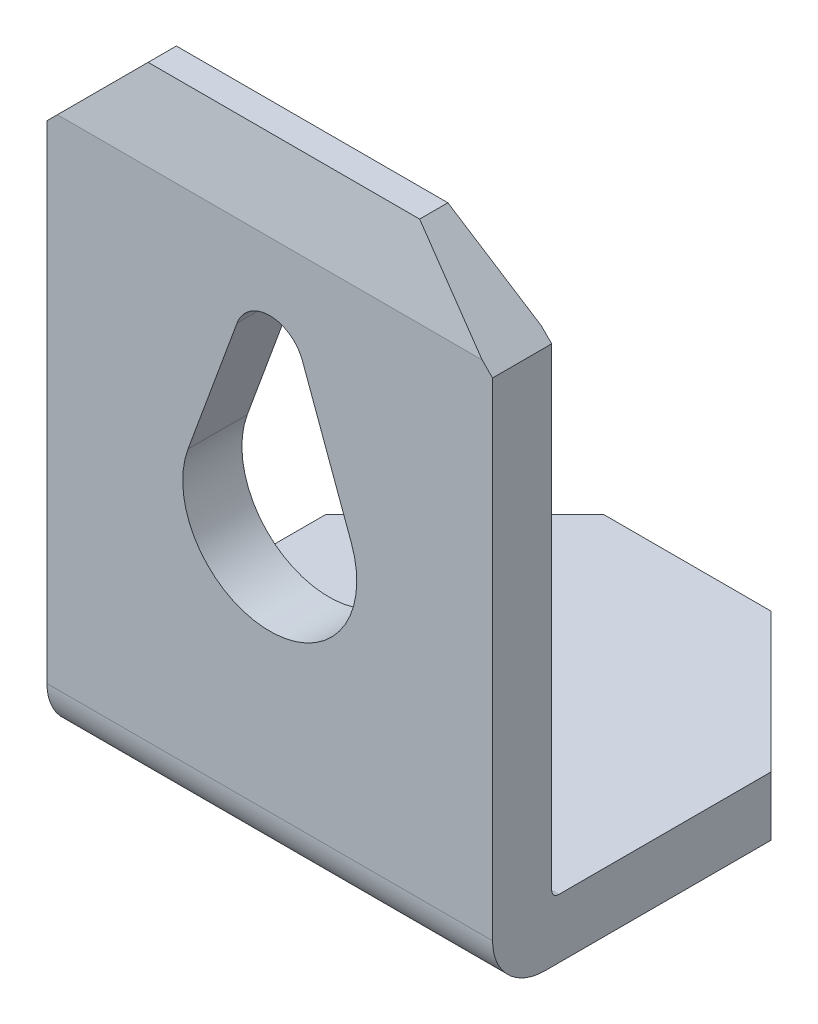
SolidWorks part; units mm, degrees
ref_plane "Front Plane" through (0, 0, 0) normal (0, 0, 1) x (1, 0, 0)
ref_plane "Top Plane" through (0, 0, 0) normal (0, 1, 0) x (1, 0, 0)
ref_plane "Right Plane" through (0, 0, 0) normal (1, 0, 0) x (0, 0, -1)
sketch "Sketch1" plane through (0, 0, 0) normal (1, 0, 0) x (0, 0, -1)
  line L0 (0, 0.1) -> (0, 7.05)
  line L1 (0, 7.05) -> (-0.2414, 8.15)
  line L2 (-0.2414, 8.15) -> (-0.6471, 8.15)
  line L3 (-0.6471, 8.15) -> (-0.85, 7.05)
  line L4 (-0.85, 7.05) -> (-0.85, -0.1)
  line L5 (-0.1, -0.85) -> (5.15, -0.85)
  line L6 (5.15, -0.85) -> (5.15, 0)
  line L7 (5.15, 0) -> (0.1, 0)
  arc A0 (-0.85, -0.1) -> (-0.1, -0.85) centre (-0.1, -0.1) ccw
  arc A1 (0, 0.1) -> (0.1, 0) centre (0.1, 0.1) ccw
  point P3 (5.15, -0.425)
  point P14 (0, 0)
  dimension "D6" = 0.75
  dimension "D7" = 0.1
  dimension "D1" = 9
  dimension "D2" = 0.85
  dimension "D3" = 1.1
  dimension "D5" = 0.85
  dimension "D4" = 6
  dimension "D8" = 0.2414
  dimension "D9" = 0.6471
extrude "Boss-Extrude1" add sketch "Sketch1" along normal blind 6.4
chamfer "Chamfer3" distance 2 angle 45 2 edges at (6.4, -0.425, -5.15) (0, -0.425, -5.15)
sketch "Sketch4" plane through (0, 0, 0.85) normal (0, 0, 1) x (1, 0, 0)
  line L0 (0, 6.9) -> (1.25, 8.15)
  line L1 (0, 7.05) -> (0, -0.1) construction
  line L2 (6.4, 8.15) -> (0, 8.15) construction
  line L4 (5.15, 8.15) -> (6.4, 6.9)
  line L5 (6.4, 7.05) -> (6.4, -0.1) construction
  line L6 (0, 6.9) -> (0, 8.15)
  line L7 (0, 8.15) -> (1.25, 8.15)
  line L8 (5.15, 8.15) -> (6.4, 8.15)
  line L9 (6.4, 8.15) -> (6.4, 6.9)
  dimension "D1" = 1.25
  dimension "D2" = 1.25
  dimension "D3" = 1.25
extrude "Cut-Extrude1" cut sketch "Sketch4" against normal up to surface (0.85 mm away) up to face at (3.2, 3.575, 0)
sketch "Sketch5" plane through (0, 0, 0.85) normal (0, 0, 1) x (1, 0, 0)
  line L0 (5.15, 8.15) -> (1.25, 8.15) construction
  line L1 (2.7306, 5.7488) -> (2.0266, 3.8307)
  line L2 (3.6696, 5.7481) -> (4.3734, 3.8307)
  line L3 (0, 6.9) -> (0, -0.1) construction
  arc A0 (2.0266, 3.8307) -> (4.3734, 3.8307) centre (3.2, 3.4) ccw
  arc A1 (3.6696, 5.7481) -> (2.7306, 5.7488) centre (3.2, 5.5765) ccw
  dimension "D1" = 2.5
  dimension "D3" = 1
  dimension "D2" = 4.75
  dimension "D4" = 2.1765
  dimension "D5" = 2.0266
  dimension "D6" = 2.7306
  dimension "D7" = 3.6696
extrude "Cut-Extrude2" cut sketch "Sketch5" against normal up to surface (0.85 mm away) up to face at (3.2, 4.6833, 0)
equation "\"D5@Sketch1\"=\"D2@Sketch1\""
